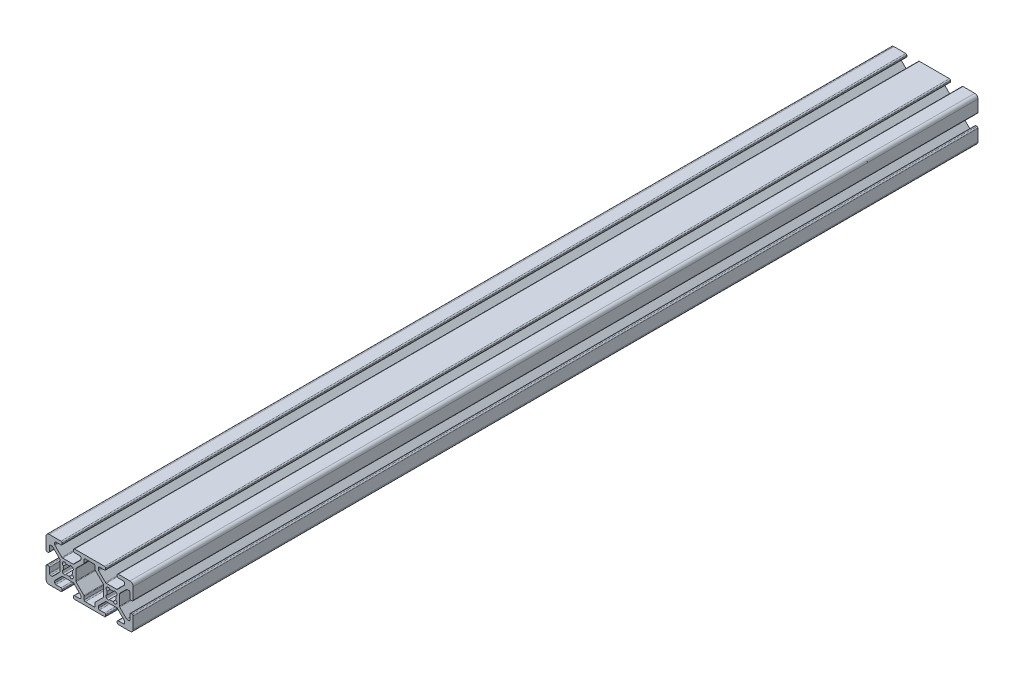
SolidWorks part; units mm, degrees
ref_plane "Front Plane" through (0, 0, 0) normal (0, 0, 1) x (1, 0, 0)
ref_plane "Top Plane" through (0, 0, 0) normal (0, 1, 0) x (1, 0, 0)
ref_plane "Right Plane" through (0, 0, 0) normal (1, 0, 0) x (0, 0, -1)
ref_plane "Plane1" through (0, 0, 4000) normal (0, 0, 1) x (1, 0, 0)
sketch "Sketch1" plane through (0, 0, 4000) normal (0, 0, 1) x (1, 0, 0)
  line L0 (-32.2198, -61.8049) -> (-32.3994, -61.9845)
  line L1 (-36.6492, -61.9845) -> (-36.8288, -61.8049)
  line L2 (-36.8288, -57.5551) -> (-36.6492, -57.3755)
  line L3 (-32.3994, -57.3755) -> (-32.2198, -57.5551)
  line L4 (-22.0193, -66.3248) -> (-22.0193, -67.672)
  line L5 (-22.5273, -68.18) -> (-26.5213, -68.18)
  line L6 (-27.0293, -67.672) -> (-27.0293, -66.3248)
  line L7 (-27.1781, -65.9655) -> (-30.7205, -62.4231)
  line L8 (-30.8693, -62.0639) -> (-30.8693, -57.2961)
  line L9 (-30.7205, -56.9369) -> (-27.1781, -53.3944)
  line L10 (-27.0293, -53.0352) -> (-27.0293, -51.688)
  line L11 (-26.5213, -51.18) -> (-22.5273, -51.18)
  line L12 (-22.0193, -51.688) -> (-22.0193, -53.0352)
  line L13 (-21.8705, -53.3944) -> (-18.3281, -56.9369)
  line L14 (-18.1793, -57.2961) -> (-18.1793, -62.0639)
  line L15 (-18.3281, -62.4231) -> (-21.8705, -65.9655)
  line L16 (-12.2198, -61.8049) -> (-12.3994, -61.9845)
  line L17 (-16.6492, -61.9845) -> (-16.8288, -61.8049)
  line L18 (-16.8288, -57.5551) -> (-16.6492, -57.3755)
  line L19 (-12.3994, -57.3755) -> (-12.2198, -57.5551)
  line L20 (-40.3705, -66.5869) -> (-37.2674, -63.4838)
  line L21 (-36.9082, -63.335) -> (-32.1404, -63.335)
  line L22 (-31.7812, -63.4838) -> (-28.6781, -66.5869)
  line L23 (-28.5293, -66.9461) -> (-28.5293, -67.672)
  line L24 (-29.0373, -68.18) -> (-31.3863, -68.18)
  line L25 (-31.8943, -68.688) -> (-31.8943, -69.172)
  line L26 (-31.3863, -69.68) -> (-17.6623, -69.68)
  line L27 (-17.1543, -69.172) -> (-17.1543, -68.688)
  line L28 (-17.6623, -68.18) -> (-20.0113, -68.18)
  line L29 (-20.5193, -67.672) -> (-20.5193, -66.9461)
  line L30 (-20.3705, -66.5869) -> (-17.2674, -63.4838)
  line L31 (-16.9082, -63.335) -> (-12.1404, -63.335)
  line L32 (-11.7812, -63.4838) -> (-8.6781, -66.5869)
  line L33 (-8.5293, -66.9461) -> (-8.5293, -67.672)
  line L34 (-9.0373, -68.18) -> (-11.3863, -68.18)
  line L35 (-11.8943, -68.688) -> (-11.8943, -69.172)
  line L36 (-11.3863, -69.68) -> (-6.0243, -69.68)
  line L37 (-4.5243, -68.18) -> (-4.5243, -62.818)
  line L38 (-5.0323, -62.31) -> (-5.5163, -62.31)
  line L39 (-6.0243, -62.818) -> (-6.0243, -65.167)
  line L40 (-6.5323, -65.675) -> (-7.2582, -65.675)
  line L41 (-7.6174, -65.5262) -> (-10.7205, -62.4231)
  line L42 (-10.8693, -62.0639) -> (-10.8693, -57.2961)
  line L43 (-10.7205, -56.9369) -> (-7.6174, -53.8338)
  line L44 (-7.2582, -53.685) -> (-6.5323, -53.685)
  line L45 (-6.0243, -54.193) -> (-6.0243, -56.542)
  line L46 (-5.5163, -57.05) -> (-5.0323, -57.05)
  line L47 (-4.5243, -56.542) -> (-4.5243, -51.18)
  line L48 (-6.0243, -49.68) -> (-11.3863, -49.68)
  line L49 (-11.8943, -50.188) -> (-11.8943, -50.672)
  line L50 (-11.3863, -51.18) -> (-9.0373, -51.18)
  line L51 (-8.5293, -51.688) -> (-8.5293, -52.4139)
  line L52 (-8.6781, -52.7731) -> (-11.7812, -55.8762)
  line L53 (-12.1404, -56.025) -> (-16.9082, -56.025)
  line L54 (-17.2674, -55.8762) -> (-20.3705, -52.7731)
  line L55 (-20.5193, -52.4139) -> (-20.5193, -51.688)
  line L56 (-20.0113, -51.18) -> (-17.6623, -51.18)
  line L57 (-17.1543, -50.672) -> (-17.1543, -50.188)
  line L58 (-17.6623, -49.68) -> (-31.3863, -49.68)
  line L59 (-31.8943, -50.188) -> (-31.8943, -50.672)
  line L60 (-31.3863, -51.18) -> (-29.0373, -51.18)
  line L61 (-28.5293, -51.688) -> (-28.5293, -52.4139)
  line L62 (-28.6781, -52.7731) -> (-31.7812, -55.8762)
  line L63 (-32.1404, -56.025) -> (-36.9082, -56.025)
  line L64 (-37.2674, -55.8762) -> (-40.3705, -52.7731)
  line L65 (-40.5193, -52.4139) -> (-40.5193, -51.688)
  line L66 (-40.0113, -51.18) -> (-37.6623, -51.18)
  line L67 (-37.1543, -50.672) -> (-37.1543, -50.188)
  line L68 (-37.6623, -49.68) -> (-43.0243, -49.68)
  line L69 (-44.5243, -51.18) -> (-44.5243, -56.542)
  line L70 (-44.0163, -57.05) -> (-43.5323, -57.05)
  line L71 (-43.0243, -56.542) -> (-43.0243, -54.193)
  line L72 (-42.5163, -53.685) -> (-41.7904, -53.685)
  line L73 (-41.4312, -53.8338) -> (-38.3281, -56.9369)
  line L74 (-38.1793, -57.2961) -> (-38.1793, -62.0639)
  line L75 (-38.3281, -62.4231) -> (-41.4312, -65.5262)
  line L76 (-41.7904, -65.675) -> (-42.5163, -65.675)
  line L77 (-43.0243, -65.167) -> (-43.0243, -62.818)
  line L78 (-43.5323, -62.31) -> (-44.0163, -62.31)
  line L79 (-44.5243, -62.818) -> (-44.5243, -68.18)
  line L80 (-43.0243, -69.68) -> (-37.6623, -69.68)
  line L81 (-37.1543, -69.172) -> (-37.1543, -68.688)
  line L82 (-37.6623, -68.18) -> (-40.0113, -68.18)
  line L83 (-40.5193, -67.672) -> (-40.5193, -66.9461)
  arc A0 (-32.3994, -61.9845) -> (-33.7203, -61.6151) centre (-32.9559, -61.428) cw
  arc A1 (-33.7203, -61.6151) -> (-35.3283, -61.6151) centre (-34.5243, -59.68) cw
  arc A2 (-35.3283, -61.6151) -> (-36.6492, -61.9845) centre (-36.0927, -61.428) cw
  arc A3 (-36.8288, -61.8049) -> (-36.4594, -60.484) centre (-36.2723, -61.2484) cw
  arc A4 (-36.4594, -60.484) -> (-36.4594, -58.876) centre (-34.5243, -59.68) cw
  arc A5 (-36.4594, -58.876) -> (-36.8288, -57.5551) centre (-36.2723, -58.1116) cw
  arc A6 (-36.6492, -57.3755) -> (-35.3283, -57.7449) centre (-36.0927, -57.932) cw
  arc A7 (-35.3283, -57.7449) -> (-33.7203, -57.7449) centre (-34.5243, -59.68) cw
  arc A8 (-33.7203, -57.7449) -> (-32.3994, -57.3755) centre (-32.9559, -57.932) cw
  arc A9 (-32.2198, -57.5551) -> (-32.5892, -58.876) centre (-32.7763, -58.1116) cw
  arc A10 (-32.5892, -58.876) -> (-32.5892, -60.484) centre (-34.5243, -59.68) cw
  arc A11 (-32.5892, -60.484) -> (-32.2198, -61.8049) centre (-32.7763, -61.2484) cw
  arc A12 (-22.0193, -67.672) -> (-22.5273, -68.18) centre (-22.5273, -67.672) cw
  arc A13 (-26.5213, -68.18) -> (-27.0293, -67.672) centre (-26.5213, -67.672) cw
  arc A14 (-27.0293, -66.3248) -> (-27.1781, -65.9655) centre (-27.5373, -66.3248) ccw
  arc A15 (-30.7205, -62.4231) -> (-30.8693, -62.0639) centre (-30.3613, -62.0639) cw
  arc A16 (-30.8693, -57.2961) -> (-30.7205, -56.9369) centre (-30.3613, -57.2961) cw
  arc A17 (-27.1781, -53.3944) -> (-27.0293, -53.0352) centre (-27.5373, -53.0352) ccw
  arc A18 (-27.0293, -51.688) -> (-26.5213, -51.18) centre (-26.5213, -51.688) cw
  arc A19 (-22.5273, -51.18) -> (-22.0193, -51.688) centre (-22.5273, -51.688) cw
  arc A20 (-22.0193, -53.0352) -> (-21.8705, -53.3944) centre (-21.5113, -53.0352) ccw
  arc A21 (-18.3281, -56.9369) -> (-18.1793, -57.2961) centre (-18.6873, -57.2961) cw
  arc A22 (-18.1793, -62.0639) -> (-18.3281, -62.4231) centre (-18.6873, -62.0639) cw
  arc A23 (-21.8705, -65.9655) -> (-22.0193, -66.3248) centre (-21.5113, -66.3248) ccw
  arc A24 (-12.3994, -61.9845) -> (-13.7203, -61.6151) centre (-12.9559, -61.428) cw
  arc A25 (-13.7203, -61.6151) -> (-15.3283, -61.6151) centre (-14.5243, -59.68) cw
  arc A26 (-15.3283, -61.6151) -> (-16.6492, -61.9845) centre (-16.0927, -61.428) cw
  arc A27 (-16.8288, -61.8049) -> (-16.4594, -60.484) centre (-16.2723, -61.2484) cw
  arc A28 (-16.4594, -60.484) -> (-16.4594, -58.876) centre (-14.5243, -59.68) cw
  arc A29 (-16.4594, -58.876) -> (-16.8288, -57.5551) centre (-16.2723, -58.1116) cw
  arc A30 (-16.6492, -57.3755) -> (-15.3283, -57.7449) centre (-16.0927, -57.932) cw
  arc A31 (-15.3283, -57.7449) -> (-13.7203, -57.7449) centre (-14.5243, -59.68) cw
  arc A32 (-13.7203, -57.7449) -> (-12.3994, -57.3755) centre (-12.9559, -57.932) cw
  arc A33 (-12.2198, -57.5551) -> (-12.5892, -58.876) centre (-12.7763, -58.1116) cw
  arc A34 (-12.5892, -58.876) -> (-12.5892, -60.484) centre (-14.5243, -59.68) cw
  arc A35 (-12.5892, -60.484) -> (-12.2198, -61.8049) centre (-12.7763, -61.2484) cw
  arc A36 (-40.5193, -66.9461) -> (-40.3705, -66.5869) centre (-40.0113, -66.9461) cw
  arc A37 (-37.2674, -63.4838) -> (-36.9082, -63.335) centre (-36.9082, -63.843) cw
  arc A38 (-32.1404, -63.335) -> (-31.7812, -63.4838) centre (-32.1404, -63.843) cw
  arc A39 (-28.6781, -66.5869) -> (-28.5293, -66.9461) centre (-29.0373, -66.9461) cw
  arc A40 (-28.5293, -67.672) -> (-29.0373, -68.18) centre (-29.0373, -67.672) cw
  arc A41 (-31.3863, -68.18) -> (-31.8943, -68.688) centre (-31.3863, -68.688) ccw
  arc A42 (-31.8943, -69.172) -> (-31.3863, -69.68) centre (-31.3863, -69.172) ccw
  arc A43 (-17.6623, -69.68) -> (-17.1543, -69.172) centre (-17.6623, -69.172) ccw
  arc A44 (-17.1543, -68.688) -> (-17.6623, -68.18) centre (-17.6623, -68.688) ccw
  arc A45 (-20.0113, -68.18) -> (-20.5193, -67.672) centre (-20.0113, -67.672) cw
  arc A46 (-20.5193, -66.9461) -> (-20.3705, -66.5869) centre (-20.0113, -66.9461) cw
  arc A47 (-17.2674, -63.4838) -> (-16.9082, -63.335) centre (-16.9082, -63.843) cw
  arc A48 (-12.1404, -63.335) -> (-11.7812, -63.4838) centre (-12.1404, -63.843) cw
  arc A49 (-8.6781, -66.5869) -> (-8.5293, -66.9461) centre (-9.0373, -66.9461) cw
  arc A50 (-8.5293, -67.672) -> (-9.0373, -68.18) centre (-9.0373, -67.672) cw
  arc A51 (-11.3863, -68.18) -> (-11.8943, -68.688) centre (-11.3863, -68.688) ccw
  arc A52 (-11.8943, -69.172) -> (-11.3863, -69.68) centre (-11.3863, -69.172) ccw
  arc A53 (-6.0243, -69.68) -> (-4.5243, -68.18) centre (-6.0243, -68.18) ccw
  arc A54 (-4.5243, -62.818) -> (-5.0323, -62.31) centre (-5.0323, -62.818) ccw
  arc A55 (-5.5163, -62.31) -> (-6.0243, -62.818) centre (-5.5163, -62.818) ccw
  arc A56 (-6.0243, -65.167) -> (-6.5323, -65.675) centre (-6.5323, -65.167) cw
  arc A57 (-7.2582, -65.675) -> (-7.6174, -65.5262) centre (-7.2582, -65.167) cw
  arc A58 (-10.7205, -62.4231) -> (-10.8693, -62.0639) centre (-10.3613, -62.0639) cw
  arc A59 (-10.8693, -57.2961) -> (-10.7205, -56.9369) centre (-10.3613, -57.2961) cw
  arc A60 (-7.6174, -53.8338) -> (-7.2582, -53.685) centre (-7.2582, -54.193) cw
  arc A61 (-6.5323, -53.685) -> (-6.0243, -54.193) centre (-6.5323, -54.193) cw
  arc A62 (-6.0243, -56.542) -> (-5.5163, -57.05) centre (-5.5163, -56.542) ccw
  arc A63 (-5.0323, -57.05) -> (-4.5243, -56.542) centre (-5.0323, -56.542) ccw
  arc A64 (-4.5243, -51.18) -> (-6.0243, -49.68) centre (-6.0243, -51.18) ccw
  arc A65 (-11.3863, -49.68) -> (-11.8943, -50.188) centre (-11.3863, -50.188) ccw
  arc A66 (-11.8943, -50.672) -> (-11.3863, -51.18) centre (-11.3863, -50.672) ccw
  arc A67 (-9.0373, -51.18) -> (-8.5293, -51.688) centre (-9.0373, -51.688) cw
  arc A68 (-8.5293, -52.4139) -> (-8.6781, -52.7731) centre (-9.0373, -52.4139) cw
  arc A69 (-11.7812, -55.8762) -> (-12.1404, -56.025) centre (-12.1404, -55.517) cw
  arc A70 (-16.9082, -56.025) -> (-17.2674, -55.8762) centre (-16.9082, -55.517) cw
  arc A71 (-20.3705, -52.7731) -> (-20.5193, -52.4139) centre (-20.0113, -52.4139) cw
  arc A72 (-20.5193, -51.688) -> (-20.0113, -51.18) centre (-20.0113, -51.688) cw
  arc A73 (-17.6623, -51.18) -> (-17.1543, -50.672) centre (-17.6623, -50.672) ccw
  arc A74 (-17.1543, -50.188) -> (-17.6623, -49.68) centre (-17.6623, -50.188) ccw
  arc A75 (-31.3863, -49.68) -> (-31.8943, -50.188) centre (-31.3863, -50.188) ccw
  arc A76 (-31.8943, -50.672) -> (-31.3863, -51.18) centre (-31.3863, -50.672) ccw
  arc A77 (-29.0373, -51.18) -> (-28.5293, -51.688) centre (-29.0373, -51.688) cw
  arc A78 (-28.5293, -52.4139) -> (-28.6781, -52.7731) centre (-29.0373, -52.4139) cw
  arc A79 (-31.7812, -55.8762) -> (-32.1404, -56.025) centre (-32.1404, -55.517) cw
  arc A80 (-36.9082, -56.025) -> (-37.2674, -55.8762) centre (-36.9082, -55.517) cw
  arc A81 (-40.3705, -52.7731) -> (-40.5193, -52.4139) centre (-40.0113, -52.4139) cw
  arc A82 (-40.5193, -51.688) -> (-40.0113, -51.18) centre (-40.0113, -51.688) cw
  arc A83 (-37.6623, -51.18) -> (-37.1543, -50.672) centre (-37.6623, -50.672) ccw
  arc A84 (-37.1543, -50.188) -> (-37.6623, -49.68) centre (-37.6623, -50.188) ccw
  arc A85 (-43.0243, -49.68) -> (-44.5243, -51.18) centre (-43.0243, -51.18) ccw
  arc A86 (-44.5243, -56.542) -> (-44.0163, -57.05) centre (-44.0163, -56.542) ccw
  arc A87 (-43.5323, -57.05) -> (-43.0243, -56.542) centre (-43.5323, -56.542) ccw
  arc A88 (-43.0243, -54.193) -> (-42.5163, -53.685) centre (-42.5163, -54.193) cw
  arc A89 (-41.7904, -53.685) -> (-41.4312, -53.8338) centre (-41.7904, -54.193) cw
  arc A90 (-38.3281, -56.9369) -> (-38.1793, -57.2961) centre (-38.6873, -57.2961) cw
  arc A91 (-38.1793, -62.0639) -> (-38.3281, -62.4231) centre (-38.6873, -62.0639) cw
  arc A92 (-41.4312, -65.5262) -> (-41.7904, -65.675) centre (-41.7904, -65.167) cw
  arc A93 (-42.5163, -65.675) -> (-43.0243, -65.167) centre (-42.5163, -65.167) cw
  arc A94 (-43.0243, -62.818) -> (-43.5323, -62.31) centre (-43.5323, -62.818) ccw
  arc A95 (-44.0163, -62.31) -> (-44.5243, -62.818) centre (-44.0163, -62.818) ccw
  arc A96 (-44.5243, -68.18) -> (-43.0243, -69.68) centre (-43.0243, -68.18) ccw
  arc A97 (-37.6623, -69.68) -> (-37.1543, -69.172) centre (-37.6623, -69.172) ccw
  arc A98 (-37.1543, -68.688) -> (-37.6623, -68.18) centre (-37.6623, -68.688) ccw
  arc A99 (-40.0113, -68.18) -> (-40.5193, -67.672) centre (-40.0113, -67.672) cw
extrude "Boss-Extrude1" add sketch "Sketch1" against normal blind 387.35
